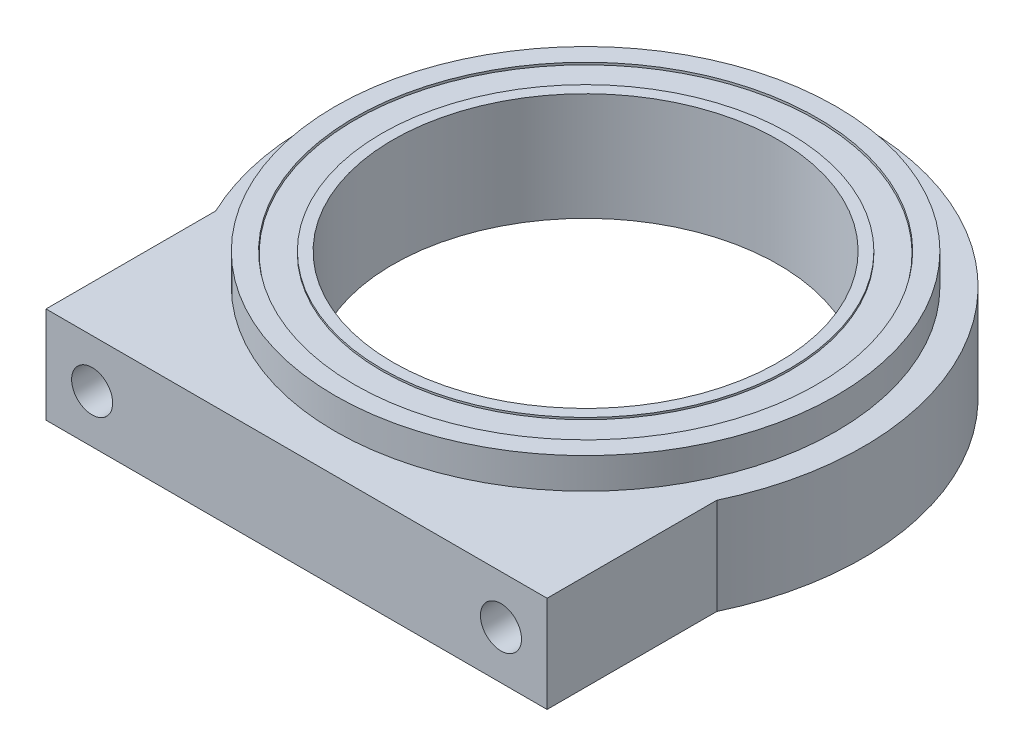
SolidWorks part; units mm, degrees
material "1060 Alloy"
ref_plane "Front Plane" through (0, 0, 0) normal (0, 0, 1) x (1, 0, 0)
ref_plane "Top Plane" through (0, 0, 0) normal (0, 1, 0) x (1, 0, 0)
ref_plane "Right Plane" through (0, 0, 0) normal (1, 0, 0) x (0, 0, -1)
sketch "Sketch1" plane through (0, 0, 0) normal (0, 1, 0) x (1, 0, 0)
  line L0 (0, 18.288) -> (0, -19.05) construction
  line L1 (-16.51, -19.05) -> (16.51, -19.05)
  line L2 (-16.51, -19.05) -> (-16.51, -7.8658)
  line L3 (16.51, -19.05) -> (16.51, -7.8658)
  arc A0 (16.51, -7.8658) -> (-16.51, -7.8658) centre (0, 0) ccw
  circle A1 centre (0, 0) radius 15.875
  dimension "D1" = 36.576
  dimension "D5" = 31.75
  dimension "D2" = 37.338
  dimension "D3" = 33.02
  dimension "D4" = 16.51
extrude "Boss-Extrude1" add sketch "Sketch1" along normal mid plane 6.35
sketch "Sketch2" plane through (0, 3.175, 0) normal (0, 1, 0) x (1, 0, 0)
  circle A0 centre (0, 0) radius 16.51
  dimension "D1" = 33.02
extrude "Cut-Extrude1" cut sketch "Sketch2" against normal blind 5.08
sketch "Sketch3" plane through (0, -1.905, 0) normal (0, 1, 0) x (1, 0, 0)
  circle A0 centre (0, 0) radius 16.51
  circle A1 centre (0, 0) radius 15.24
  dimension "D1" = 30.48
extrude "Boss-Extrude2" add sketch "Sketch3" along normal blind 7.112
sketch "Sketch4" plane through (0, 0, 0) normal (0, 1, 0) x (1, 0, 0)
  circle A0 centre (0, 0) radius 15.2111
  circle A1 centre (0, 0) radius 13.4331
  dimension "D1" = 1.778
extrude "Boss-Extrude3" add sketch "Sketch4" along normal blind 5.08 and the other way blind 1.778 separate body
sketch "Sketch5" plane through (0, 5.207, 0) normal (0, 1, 0) x (1, 0, 0)
  circle A0 centre (0, 0) radius 13.4331
  circle A1 centre (0, 0) radius 12.7
extrude "Boss-Extrude4" add sketch "Sketch5" against normal blind 7.112
sketch "Sketch6" plane through (0, 0, 19.05) normal (0, 0, 1) x (1, 0, 0)
  line L0 (0, 0) -> (0, 13.4704) construction
  line L1 (0, 13.4704) -> (-13.4704, 0) construction
  line L2 (0, 13.4704) -> (13.4704, 0) construction
  dimension "D1" = 19.05
  dimension "D2" = 19.05
  dimension "D3" = 90
  dimension "D4" = 45
hole_wizard "#6-32 Tapped Hole1" positions "Sketch8" profile "Sketch7" tap size "#6-32" standard "Ansi Inch"
sketch "Sketch8" plane through (0, 0, 19.05) normal (0, 0, 1) x (1, 0, 0)
  point P0 (13.4704, 0)
  point P1 (-13.4704, 0)
sketch "Sketch7" plane through (13.4704, 0, 19.05) normal (1, 0, 0) x (0, -1, 0)
  line L0 (0, 0) -> (0, 7.1627)
  line L1 (0, 7.1627) -> (1.3525, 6.35)
  line L2 (1.3525, 6.35) -> (1.3525, 0)
  line L5 (1.3525, 0) -> (0, 0)
  line L10 (0, 7.1627) -> (-1.3526, 6.35) construction
  line L11 (0, -6.35) -> (0, 107.95) construction
  dimension "Tap Drill Dia." = 2.7051
  dimension "Tap Drill Depth" = 6.35
  dimension "Drill Angle" = 118
cosmetic thread "Hole Thread1" parameters "D1"=6.35, "D2"=3.5052
cosmetic thread "Hole Thread2" parameters "D1"=6.35, "D2"=3.5052
